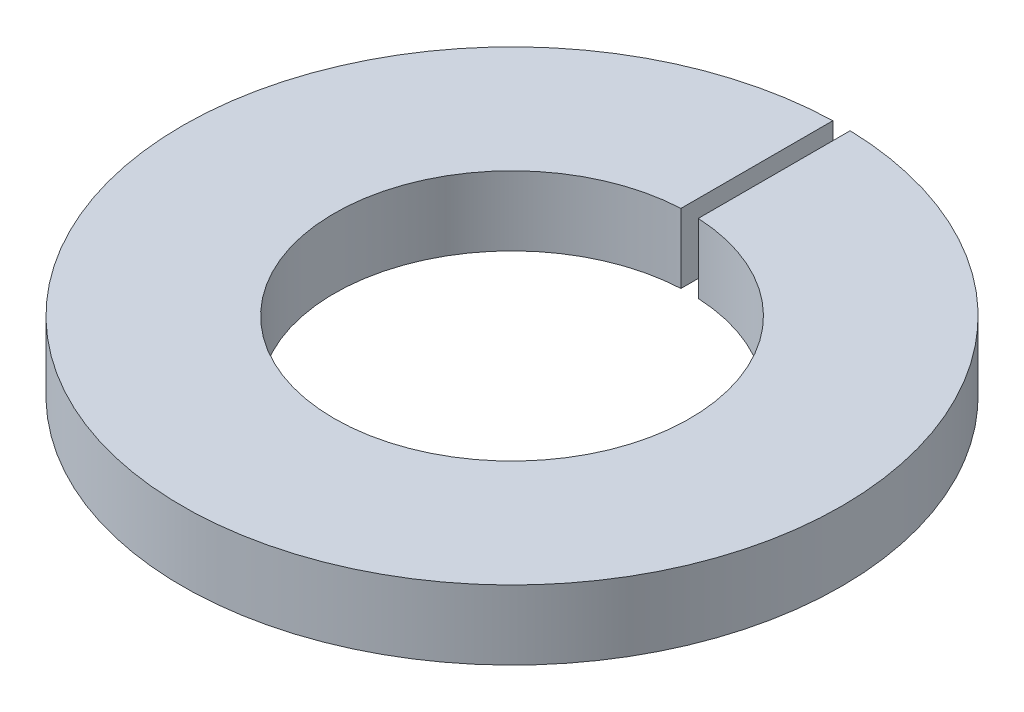
SolidWorks part; units mm, degrees
material "1.4057 (X17CrNi16-2)"
ref_plane "Plano frontal" through (0, 0, 0) normal (0, 0, 1) x (1, 0, 0)
ref_plane "Plano superior" through (0, 0, 0) normal (0, 1, 0) x (1, 0, 0)
ref_plane "Plano direito" through (0, 0, 0) normal (1, 0, 0) x (0, 0, -1)
sketch "Esboço1" plane through (0, 0, 0) normal (0, 1, 0) x (1, 0, 0)
  line L0 (-0.1, 3.7987) -> (-0.1, 2.0476)
  line L1 (0.1, 3.7987) -> (0.1, 2.0476)
  line L2 (0, 0) -> (0, 4.1585) construction
  line L3 (0.1, 2.9231) -> (0, 2.9231) construction
  line L4 (0, 2.9231) -> (-0.1, 2.9231) construction
  arc A2 (-0.1, 2.0476) -> (0.1, 2.0476) centre (0, 0) ccw
  arc A3 (-0.1, 3.7987) -> (0.1, 3.7987) centre (0, 0) ccw
  dimension "D1" = 2.05
  dimension "D2" = 3.8
  dimension "D3" = 0.2
extrude "Ressalto-extrusão1" add sketch "Esboço1" along normal blind 0.8
